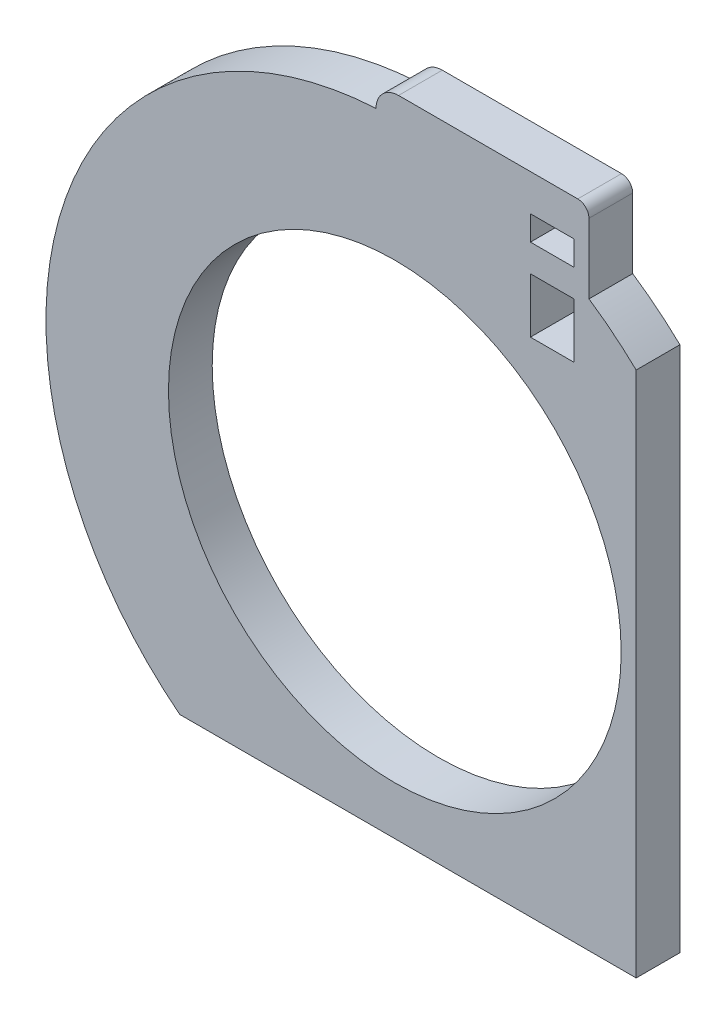
SolidWorks part; units mm, degrees
ref_plane "Front" through (0, 0, 0) normal (0, 0, 1) x (1, 0, 0)
ref_plane "Top" through (0, 0, 0) normal (0, 1, 0) x (1, 0, 0)
ref_plane "Right" through (0, 0, 0) normal (1, 0, 0) x (0, 0, -1)
sketch "Sketch1" plane through (0, 0, 0) normal (0, 0, 1) x (1, 0, 0)
  line L0 (27.5855, 49.4579) -> (27.5855, -33.8929) construction
  line L1 (27.5855, -31.3929) -> (-24.5769, -31.3929)
  line L2 (27.5855, -31.3929) -> (27.5855, 28.7851)
  line L3 (0, 0) -> (0, -31.3929) construction
  line L4 (0, -27.3855) -> (-13.3401, -27.3855) construction
  line L6 (20.9107, 42.3835) -> (0.4271, 42.3835)
  line L7 (0, -27.3855) -> (13.3401, -27.3855) construction
  line L8 (9.9875, -24.8855) -> (16.6928, -29.8855) construction
  line L9 (-9.9875, -29.8855) -> (-16.6928, -29.8855) construction
  line L10 (-9.9875, -29.8855) -> (-9.9875, -24.8855) construction
  line L11 (-9.9875, -24.8855) -> (-16.6928, -24.8855) construction
  line L12 (-16.6928, -29.8855) -> (-16.6928, -24.8855) construction
  line L13 (-9.9875, -29.8855) -> (-16.6928, -24.8855) construction
  line L14 (-9.9875, -24.8855) -> (-16.6928, -29.8855) construction
  line L15 (9.9875, -29.8855) -> (16.6928, -24.8855) construction
  line L16 (16.6928, -29.8855) -> (16.6928, -24.8855) construction
  line L17 (9.9875, -24.8855) -> (16.6928, -24.8855) construction
  line L18 (9.9875, -29.8855) -> (9.9875, -24.8855) construction
  line L19 (9.9875, -29.8855) -> (16.6928, -29.8855) construction
  line L20 (22.1896, 41.1045) -> (22.1896, 33.1234)
  circle A0 centre (0, 0) radius 25.869
  arc A1 (27.5855, 28.7851) -> (22.1896, 33.1234) centre (0, 0) ccw
  circle A2 centre (0, 0) radius 25.869 construction
  arc A3 (0.4271, 42.3835) -> (-2.1451, 39.8113) centre (0.4271, 39.8113) ccw
  arc A4 (22.1896, 41.1045) -> (20.9107, 42.3835) centre (20.9107, 41.1045) ccw
  arc A5 (-2.1451, 39.8113) -> (-24.5769, -31.3929) centre (0, 0) ccw
  dimension "D1" = 14
  dimension "D3" = 5
extrude "Boss-Extrude1" add sketch "Sketch1" along normal blind 5
sketch "Sketch2" plane through (0, 0, 0) normal (0, 0, -1) x (-1, 0, 0)
  line L0 (0, 0) -> (0, 1.022) construction
  line L1 (0, 0) -> (0, 39.869) construction
  line L2 (-18, 36.8037) -> (-18, 13.4674) construction
  line L4 (-20.5, 38.2072) -> (-15.5, 38.2072)
  line L5 (-20.5, 38.2072) -> (-20.5, 35.4002)
  line L6 (-20.5, 35.4002) -> (-15.5, 35.4002)
  line L7 (-15.5, 38.2072) -> (-15.5, 35.4002)
  line L8 (-20.5, 38.2072) -> (-15.5, 35.4002) construction
  line L9 (-20.5, 35.4002) -> (-15.5, 38.2072) construction
  line L10 (-20.5, 32.2687) -> (-15.5, 32.2687)
  line L11 (-20.5, 32.2687) -> (-20.5, 25.9958)
  line L12 (-20.5, 25.9958) -> (-15.5, 25.9958)
  line L13 (-15.5, 32.2687) -> (-15.5, 25.9958)
  line L14 (-20.5, 32.2687) -> (-15.5, 25.9958) construction
  line L15 (-20.5, 25.9958) -> (-15.5, 32.2687) construction
  arc A0 (-22.1896, 33.1234) -> (-27.5855, 28.7851) centre (0, 0) ccw construction
  point P14 (-18, 29.1322)
  dimension "D1" = 5
  dimension "D2" = 18
extrude "Cut-Extrude1" cut sketch "Sketch2" against normal up to next
